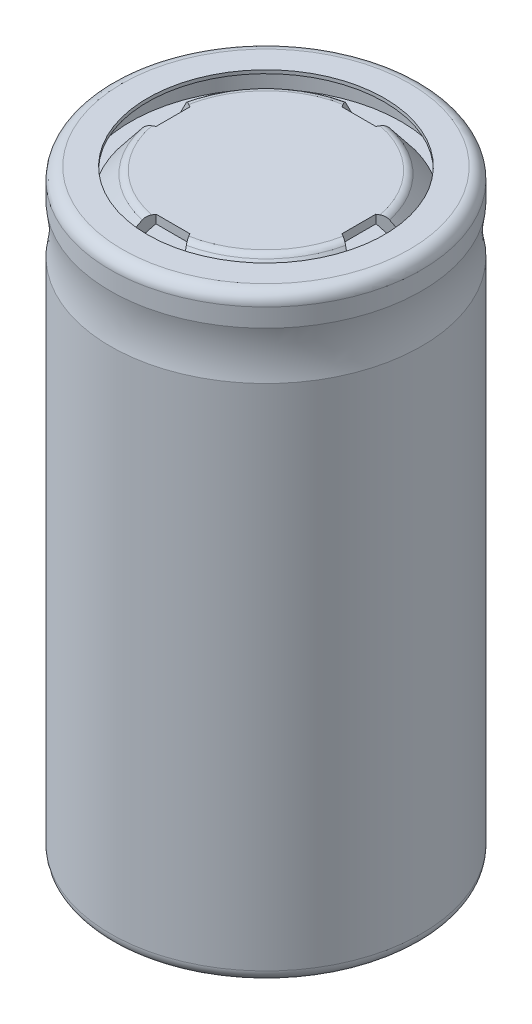
SolidWorks part; units mm, degrees
ref_plane "Спереди" through (0, 0, 0) normal (0, 0, 1) x (1, 0, 0)
ref_plane "Сверху" through (0, 0, 0) normal (0, 1, 0) x (1, 0, 0)
ref_plane "Справа" through (0, 0, 0) normal (1, 0, 0) x (0, 0, -1)
sketch "Эскиз1" plane through (0, 0, 0) normal (0, 0, 1) x (1, 0, 0)
  line L0 (0, 0) -> (0, 113.9204) construction
  line L1 (0, 0) -> (8.5, 0)
  line L2 (9, 0.5) -> (9, 30.5873)
  line L3 (8.5, 30.5873) -> (8.5, 0.5)
  line L4 (8.4985, 35.0015) -> (10.3122, 35.0015) construction
  line L5 (9, 33.4157) -> (9, 34.5)
  line L6 (0, 0) -> (0, 0.5)
  line L7 (0, 0.5) -> (8.5, 0.5)
  line L8 (7.997, 34.5) -> (7.997, 33.5)
  line L9 (8.4985, 33.4152) -> (8.4985, 34.5)
  line L10 (7.997, 33.5) -> (8.4985, 33.5)
  line L11 (8.4985, 35.0015) -> (-1.0683, 35.0015) construction
  line L12 (0, 35) -> (5.7595, 35.0014)
  line L13 (0, 35) -> (0, 34.5)
  line L14 (7.997, 33.5) -> (7.2, 33.5)
  line L15 (7.2, 33.5) -> (6.1502, 34.8136)
  line L16 (0, 34.5) -> (5.6088, 34.5)
  line L17 (7.2, 33.5) -> (7.2, 33)
  line L18 (7.2, 33) -> (8.2, 33)
  line L19 (8.2, 33) -> (8.2, 33.5)
  line L20 (5.6088, 34.5) -> (6.7, 33.5)
  line L21 (7.2, 33.5) -> (0, 33.5)
  line L22 (0, 33.5) -> (0, 33)
  line L23 (0, 33) -> (7.2, 33)
  arc A0 (9, 0.5) -> (8.5, 0) centre (8.5, 0.5) cw
  arc A1 (9, 34.5) -> (7.997, 34.5) centre (8.4985, 34.5) ccw
  arc A2 (8.6667, 32.9443) -> (8.6667, 31.0587) centre (9, 32.0015) ccw
  arc A3 (9, 33.4157) -> (8.6667, 32.9443) centre (8.5, 33.4157) cw
  arc A4 (9, 30.5873) -> (8.6667, 31.0587) centre (8.5, 30.5873) ccw
  arc A5 (8.1657, 32.9439) -> (8.1667, 31.0587) centre (8.5, 32.0015) ccw
  arc A6 (8.1667, 31.0587) -> (8.5, 30.5873) centre (8, 30.5873) cw
  arc A7 (8.4985, 33.4152) -> (8.1657, 32.9439) centre (7.9985, 33.4152) cw
  arc A8 (5.7595, 35.0014) -> (6.1502, 34.8136) centre (5.7596, 34.5014) cw
  point P7 (9, 0)
  point P18 (9, 33.0015)
  point P30 (8.4985, 33.0015)
  point P43 (6, 35.0015)
  dimension "D3" = 0.5
  dimension "D4" = 0.5015
  dimension "D5" = 1
  dimension "D7" = 0.5
  dimension "D8" = 0.5
  dimension "D14" = 1
  dimension "D12" = 0.5
  dimension "D16" = 0.5
  dimension "D24" = 0.5
  dimension "D1" = 18
  dimension "D2" = 34.5
  dimension "D6" = 2
  dimension "D9" = 2.4985
  dimension "D10" = 0.5
  dimension "D11" = 8.5
  dimension "D13" = 1
  dimension "D15" = 2.4985
  dimension "D17" = 0.5
  dimension "D18" = 12
  dimension "D19" = 0.5
  dimension "D20" = 0.5
  dimension "D21" = 1
  dimension "D22" = 0.8
  dimension "D23" = 5.6088
  dimension "D25" = 0.5
  dimension "D26" = 1
revolve "Повернуть1" add sketch "Эскиз1" angle 360 about L0
sketch "Эскиз2" plane through (0, 34.5, 0) normal (0, -1, 0) x (1, 0, 0)
  line L0 (0, -10.6971) -> (0, 9.7635) construction
  line L1 (-14.6111, 0) -> (9.951, 0) construction
  line L2 (-1, -5.4957) -> (1, -5.4957)
  line L3 (1, -5.4957) -> (2, -7.2)
  line L4 (2, -7.2) -> (-2, -7.2)
  line L5 (-1, -5.4957) -> (-2, -7.2)
  line L6 (-5.4957, 1) -> (-5.4957, -1)
  line L7 (-5.4957, -1) -> (-7.2, -2)
  line L8 (-7.2, -2) -> (-7.2, 2)
  line L9 (-5.4957, 1) -> (-7.2, 2)
  line L10 (1, 5.4957) -> (-1, 5.4957)
  line L11 (-1, 5.4957) -> (-2, 7.2)
  line L12 (-2, 7.2) -> (2, 7.2)
  line L13 (1, 5.4957) -> (2, 7.2)
  line L14 (5.4957, -1) -> (5.4957, 1)
  line L15 (5.4957, 1) -> (7.2, 2)
  line L16 (7.2, 2) -> (7.2, -2)
  line L17 (5.4957, -1) -> (7.2, -2)
  point P12 (0, -7.2)
  point P13 (0, -5.4957)
  point P20 (-7.2, 0)
  point P21 (-5.4957, 0)
  point P26 (0, 7.2)
  point P27 (0, 5.4957)
  point P32 (7.2, 0)
  point P33 (5.4957, 0)
  dimension "D1" = 1.7043
  dimension "D2" = 2
  dimension "D3" = 1
  dimension "D5" = 5.4957
  dimension "D4" = 4
extrude "Вырез-Вытянуть1" cut sketch "Эскиз2" along normal up to surface (1 mm away) and the other way through all up to face at (0, 33.5, -7.997)
sketch "Эскиз3" plane through (0, 0, 0) normal (0, 0, 1) x (1, 0, 0)
  line L0 (0, -2.74) -> (0, 74.3076) construction
  line L1 (9, 34.5) -> (9, 33.4157)
  line L2 (8.4977, 0) -> (7, 0)
  line L3 (9, 34.5) -> (9, 33.4157)
  line L4 (9, 30.5873) -> (9, 0.5)
  line L5 (9, 30.5873) -> (9, 0.5)
  line L6 (8.5953, 0.0092) -> (8.4977, 0)
  line L7 (8.5953, 0.0092) -> (8.4977, 0)
  line L8 (8.4977, 0) -> (-8.5, 0)
  line L10 (-9, 0.5) -> (-9, 30.5873)
  line L12 (-9, 33.4157) -> (-9, 34.5)
  line L14 (-8.5941, 34.9923) -> (8.4962, 35.0015)
  line L16 (-8.5, 0) -> (8.5, 0) construction
  line L17 (7, 0) -> (7, -0.2)
  line L18 (7, -0.2) -> (8.5, -0.2)
  line L19 (9.2, 0.5) -> (9.2, 30.5873)
  line L20 (8.4985, 34.5) -> (8.4985, 65.4748) construction
  line L21 (9.2, 33.4163) -> (9.2, 34.5)
  line L22 (9, 0.5) -> (9.2, 0.5) construction
  line L23 (7, 35.0015) -> (8.4962, 35.0015)
  line L24 (8.4985, 35.0015) -> (-8.4985, 35.0015) construction
  line L25 (7, 35.0015) -> (7, 35.2015)
  line L26 (7, 35.2015) -> (8.4985, 35.2015)
  arc A0 (8.6667, 32.9443) -> (9, 33.4157) centre (8.5, 33.4157) ccw
  arc A2 (8.6667, 32.9443) -> (8.6667, 31.0587) centre (9, 32.0015) ccw
  arc A4 (9, 30.5873) -> (8.6667, 31.0587) centre (8.5, 30.5873) ccw
  arc A6 (8.5953, 0.0092) -> (9, 0.5) centre (8.5, 0.5) ccw
  arc A7 (8.5953, 0.0092) -> (9, 0.5) centre (8.5, 0.5) ccw
  arc A8 (-9, 0.5) -> (-8.5, 0) centre (-8.5, 0.5) ccw
  arc A10 (-8.6667, 31.0587) -> (-9, 30.5873) centre (-8.5, 30.5873) ccw
  arc A12 (-8.6667, 31.0587) -> (-8.6667, 32.9443) centre (-9, 32.0015) ccw
  arc A14 (-9, 33.4157) -> (-8.6667, 32.9443) centre (-8.5, 33.4157) ccw
  arc A16 (-8.5941, 34.9923) -> (-9, 34.5) centre (-8.4985, 34.5) ccw
  arc A18 (9, 34.5) -> (8.4962, 35.0015) centre (8.4985, 34.5) ccw
  arc A19 (9, 34.5) -> (8.4962, 35.0015) centre (8.4985, 34.5) ccw
  arc A21 (8.4985, 35.2015) -> (9.2, 34.5) centre (8.4985, 34.5) cw
  arc A22 (8.5, -0.2) -> (9.2, 0.5) centre (8.5, 0.5) ccw
  spline S0 degree 2 poles (9, 33.4157) (8.6971, 31.9443) (9, 30.5873) knots 0 0 0 0.587528 0.587528 0.587528
  spline S1 degree 2 poles (9.2, 33.4163) (8.9014, 31.9539) (9.2, 30.5873) knots 0 0 0 0.679955 0.679955 0.679955
  dimension "D1" = 7
  dimension "D2" = 0.2
  dimension "D5" = 0.2
  dimension "D7" = 34
  dimension "D4" = 34
  dimension "D6" = 7
  dimension "D8" = 0.2
revolve "Повернуть4" add sketch "Эскиз3" angle 360 about L0
equation "\"D8@Эскиз1\"=\"D7@Эскиз1\""
equation "\"D14@Эскиз1\"=\"D5@Эскиз1\""
equation "\"D15@Эскиз1\"=\"D9@Эскиз1\""
equation "\"D12@Эскиз1\"=\"D7@Эскиз1\""
equation "\"D16@Эскиз1\"=\"D7@Эскиз1\""
equation "\"D17@Эскиз1\"=\"D10@Эскиз1\""
equation "\"D7@Эскиз3\"=\"D4@Эскиз3\""
equation "\"D8@Эскиз3\"=\"D5@Эскиз3\""
